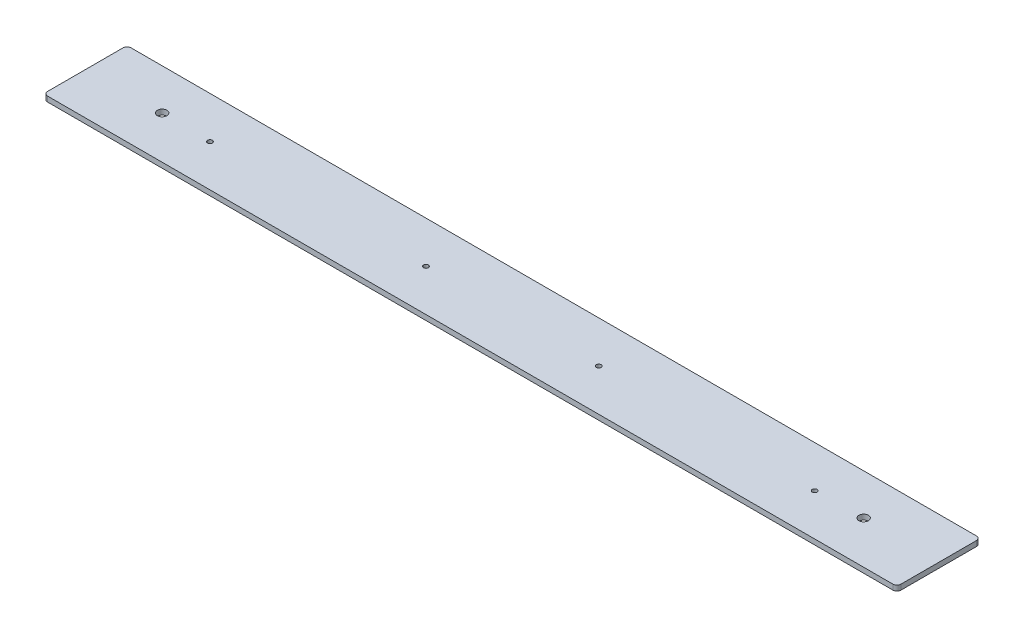
SolidWorks part; units mm, degrees
ref_plane "Front Plane" through (0, 0, 0) normal (0, 0, 1) x (1, 0, 0)
ref_plane "Top Plane" through (0, 0, 0) normal (0, 1, 0) x (1, 0, 0)
ref_plane "Right Plane" through (0, 0, 0) normal (1, 0, 0) x (0, 0, -1)
sketch "Sketch1" plane through (0, 0, 0) normal (0, 1, 0) x (1, 0, 0)
  line L1 (-259.5563, -25.4) -> (259.5562, -25.4)
  line L2 (-259.5563, -25.4) -> (-259.5563, 25.4)
  line L3 (-259.5563, 25.4) -> (259.5562, 25.4)
  line L4 (259.5562, -25.4) -> (259.5562, 25.4)
  line L5 (-259.5563, -25.4) -> (259.5562, 25.4) construction
  line L6 (-259.5563, 25.4) -> (259.5562, -25.4) construction
  point P0 (0, 0)
  dimension "D1" = 519.1125
  dimension "D2" = 50.8
extrude "Boss-Extrude1" add sketch "Sketch1" along normal blind 3.175
fillet "Fillet1" radius 2.54 4 edges at (-259.5563, 1.5875, -25.4) (-259.5563, 1.5875, 25.4) (259.5562, 1.5875, -25.4) (259.5562, 1.5875, 25.4)
hole_wizard "#4 Clearance Hole1" positions "Sketch2" profile "Sketch3" hole size "#4" standard "ANSI Inch" end condition through all
sketch "Sketch2" plane through (0, 3.175, 0) normal (0, 1, 0) x (1, 0, 0)
  point P0 (184.1103, 0)
  point P3 (52.7447, 0)
  point P6 (-52.3478, 0)
  point P9 (-183.7134, 0)
sketch "Sketch3" plane through (184.1103, 3.175, 0) normal (1, 0, 0) x (0, 0, 1)
  line L0 (0, 0) -> (0, 3.175)
  line L1 (0, 3.175) -> (1.4732, 3.175)
  line L2 (1.4732, 3.175) -> (1.4732, 0)
  line L5 (1.4732, 0) -> (0, 0)
  line L11 (0, -6.35) -> (0, 107.95) construction
  dimension "Thru Hole Dia." = 2.9464
  dimension "Thru Hole Depth" = 3.175
hole_wizard "#1 (0.228) Diameter Hole1" positions "Sketch6" profile "Sketch5" hole size "#1" standard "ANSI Inch" end condition through all
sketch "Sketch6" plane through (0, 0, 0) normal (0, -1, 0) x (-1, 0, 0)
  point P0 (-213.36, 0.5444)
  point P3 (213.36, 0.5444)
sketch "Sketch5" plane through (213.36, 0, -0.5444) normal (1, 0, 0) x (0, 0, -1)
  line L0 (0, 0) -> (0, 3.175)
  line L1 (0, 3.175) -> (2.8956, 3.175)
  line L2 (2.8956, 3.175) -> (2.8956, 0)
  line L5 (2.8956, 0) -> (0, 0)
  line L11 (0, -6.35) -> (0, 107.95) construction
  dimension "Thru Hole Dia." = 5.7912
  dimension "Thru Hole Depth" = 3.175
